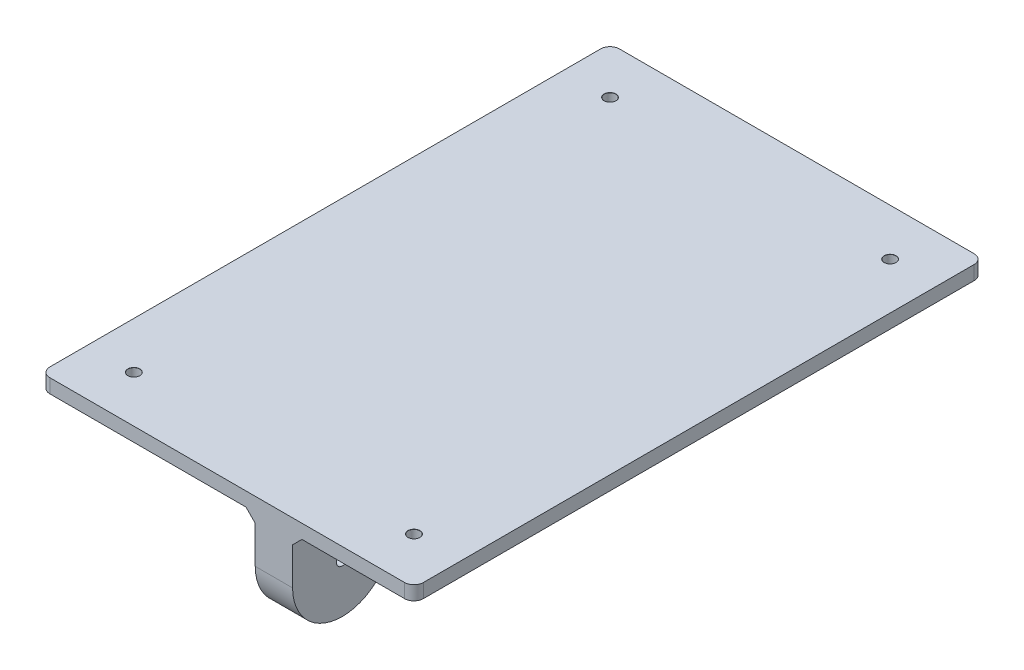
SolidWorks part; units mm, degrees
material "ABS"
ref_plane "Front Plane" through (0, 0, 0) normal (0, 0, 1) x (1, 0, 0)
ref_plane "Top Plane" through (0, 0, 0) normal (0, 1, 0) x (1, 0, 0)
ref_plane "Right Plane" through (0, 0, 0) normal (1, 0, 0) x (0, 0, -1)
sketch "Sketch1" plane through (0, 0, 0) normal (0, 1, 0) x (1, 0, 0)
  line L0 (-19.4927, 0) -> (33.7086, 0) construction
  line L1 (-40, -61) -> (40, -61)
  line L2 (-40, -61) -> (-40, 61)
  line L3 (-40, 61) -> (40, 61)
  line L4 (40, -61) -> (40, 61)
  line L5 (0, 23.6315) -> (0, -27.4954) construction
  point P0 (0, 0)
  dimension "D1" = 80
  dimension "D2" = 122
extrude "Boss-Extrude1" add sketch "Sketch1" along normal blind 3
ref_plane "Plane1" through (6, 0, 0) normal (1, 0, 0) x (0, 0, -1)
sketch "Sketch3" plane through (6, 0, 0) normal (1, 0, 0) x (0, 0, -1)
  line L0 (-61, 0) -> (-61, -10)
  line L1 (-61, 0) -> (-39.72, 0)
  line L2 (-39.72, 0) -> (-39.72, -10)
  line L3 (61, 0) -> (61, -10)
  line L4 (61, 3) -> (61, 0) construction
  line L5 (61, 0) -> (39.72, 0)
  line L6 (-61, 0) -> (61, 0) construction
  line L7 (39.72, 0) -> (39.72, -10)
  arc A0 (-61, -10) -> (-39.72, -10) centre (-50.36, -10) ccw
  arc A1 (39.72, -10) -> (61, -10) centre (50.36, -10) ccw
  dimension "D1" = 21.28
  dimension "D2" = 10
extrude "Boss-Extrude2" add sketch "Sketch3" along normal blind 8
sketch "Sketch4" plane through (6, 0, 0) normal (-1, 0, 0) x (0, 0, 1)
  circle A0 centre (-50.36, -10) radius 6.45
  circle A1 centre (50.36, -10) radius 6.45
  arc A2 (-61, -10) -> (-39.72, -10) centre (-50.36, -10) ccw construction
  arc A3 (39.72, -10) -> (61, -10) centre (50.36, -10) ccw construction
  dimension "D1" = 12.9
extrude "Cut-Extrude1" cut sketch "Sketch4" against normal blind 6
chamfer "Chamfer1" distance 2 angle 45 6 edges at (6, 0, 50.36) (10, 0, 39.72) (14, 0, 50.36) (6, 0, -50.36) (10, 0, -39.72) (14, 0, -50.36)
fillet "Fillet1" radius 2 4 edges at (40, 1.5, -61) (40, 1.5, 61) (-40, 1.5, 61) (-40, 1.5, -61)
hole_wizard "Ø2.5mm Dowel Hole1" positions "Sketch5" profile "Sketch6" hole size "Ø2.5" standard "ANSI Metric"
sketch "Sketch5" plane through (0, 3, 0) normal (0, 1, 0) x (1, 0, 0)
  line L0 (38, 61) -> (-38, 61) construction
  line L1 (-40, 59) -> (-40, -59) construction
  line L2 (-38, -61) -> (38, -61) construction
  line L3 (40, -59) -> (40, 59) construction
  point P0 (-30, 51)
  point P2 (-30, -51)
  point P4 (30, -51)
  point P6 (30, 51)
  point P12 (0, 0)
  point P13 (0, 0)
  point P14 (0, 0)
  point P15 (0, 0)
  dimension "D1" = 10
  dimension "D2" = 10
  dimension "D3" = 10
  dimension "D4" = 10
sketch "Sketch6" plane through (-30, 3, -51) normal (1, 0, 0) x (0, 0, 1)
  line L0 (0, 0) -> (0, 5.7511)
  line L1 (0, 5.7511) -> (1.25, 5)
  line L2 (1.25, 5) -> (1.25, 0.025)
  line L3 (1.25, 0.025) -> (1.275, 0)
  line L5 (1.275, 0) -> (0, 0)
  line L6 (-1.25, 0.025) -> (-1.275, 0) construction
  line L10 (0, 5.7511) -> (-1.25, 5) construction
  line L11 (0, -6.35) -> (0, 107.95) construction
  dimension "Hole Dia." = 2.5
  dimension "Hole Depth" = 5
  dimension "Near C'Sink Dia." = 2.55
  dimension "Near C'Sink Angle" = 90
  dimension "Drill Angle" = 118
hole_wizard "Ø2.5mm Dowel Hole2" positions "Sketch7" profile "Sketch8" hole size "Ø2.5" standard "ANSI Metric"
sketch "Sketch7" plane through (12, 0, 0) normal (-1, 0, 0) x (0, 0, 1)
  point P0 (-50.36, -10)
  point P3 (50.36, -10)
sketch "Sketch8" plane through (12, -10, -50.36) normal (0, 1, 0) x (0, 0, 1)
  line L0 (0, 0) -> (0, 5.7511)
  line L1 (0, 5.7511) -> (1.25, 5)
  line L2 (1.25, 5) -> (1.25, 0.025)
  line L3 (1.25, 0.025) -> (1.275, 0)
  line L5 (1.275, 0) -> (0, 0)
  line L6 (-1.25, 0.025) -> (-1.275, 0) construction
  line L10 (0, 5.7511) -> (-1.25, 5) construction
  line L11 (0, -6.35) -> (0, 107.95) construction
  dimension "Hole Dia." = 2.5
  dimension "Hole Depth" = 5
  dimension "Near C'Sink Dia." = 2.55
  dimension "Near C'Sink Angle" = 90
  dimension "Drill Angle" = 118
